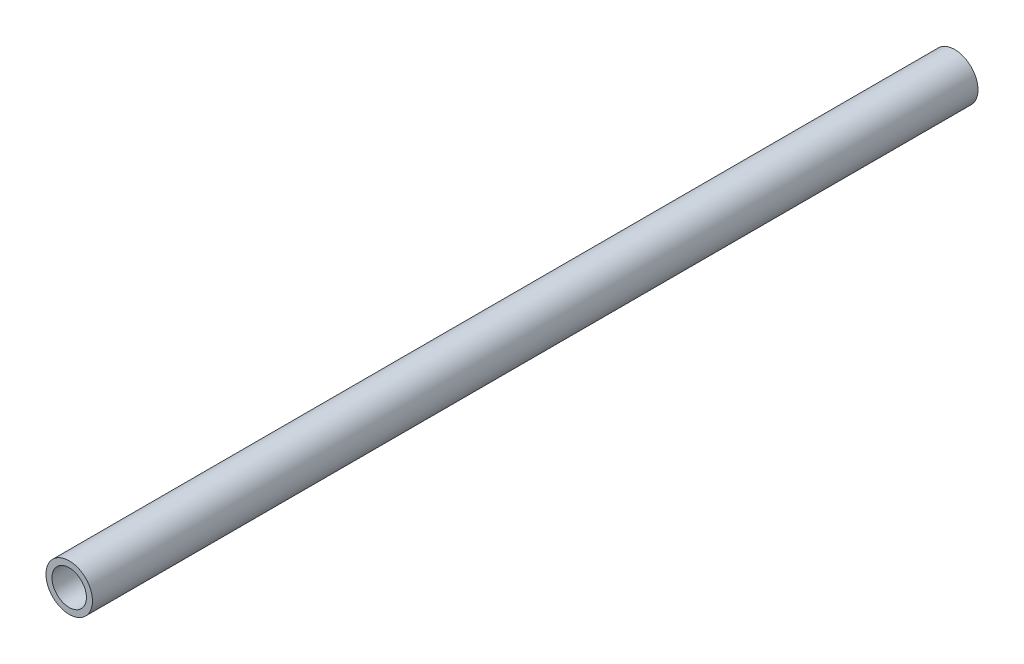
SolidWorks part; units mm, degrees
ref_plane "Front Plane" through (0, 0, 0) normal (0, 0, 1) x (1, 0, 0)
ref_plane "Top Plane" through (0, 0, 0) normal (0, 1, 0) x (1, 0, 0)
ref_plane "Right Plane" through (0, 0, 0) normal (1, 0, 0) x (0, 0, -1)
sketch "Sketch1" plane through (0, 0, 0) normal (0, 0, 1) x (1, 0, 0)
  circle A0 centre (0, 0) radius 10.668
  dimension "Pipe OD" = 21.336
extrude "Extrude-Thin1" add sketch "Sketch1" along normal mid plane 406.5 thin thin type one direction reverse wall 2.7686
